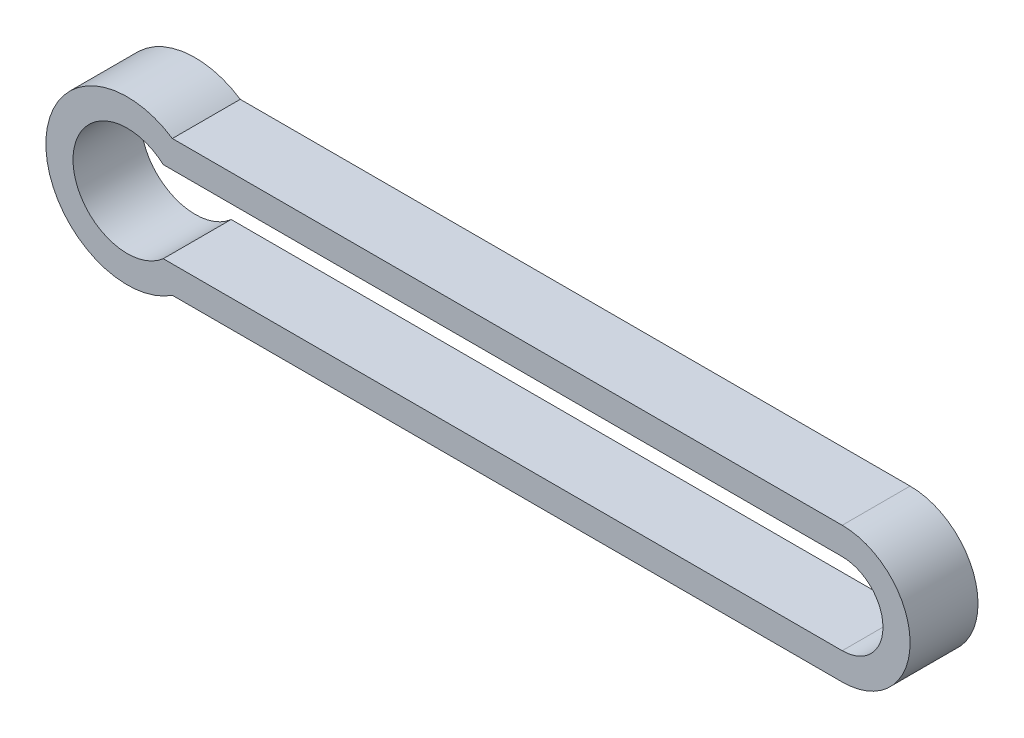
SolidWorks part; units mm, degrees
ref_plane "Front" through (0, 0, 0) normal (0, 0, 1) x (1, 0, 0)
ref_plane "Top" through (0, 0, 0) normal (0, 1, 0) x (1, 0, 0)
ref_plane "Right" through (0, 0, 0) normal (1, 0, 0) x (0, 0, -1)
sketch "草图1" plane through (0, 0, 0) normal (0, 0, 1) x (1, 0, 0)
  line L0 (2.6458, 3) -> (52.6458, 3)
  line L6 (2.6458, -3) -> (52.6458, -3)
  line L9 (52.6458, -5) -> (3.3166, -5)
  line L10 (52.6458, 5) -> (3.3166, 5)
  arc A1 (2.6458, 3) -> (2.6458, -3) centre (0, 0) ccw
  arc A9 (52.6458, -3) -> (52.6458, 3) centre (52.6458, 0) ccw
  arc A11 (3.3166, 5) -> (3.3166, -5) centre (0, 0) ccw
  arc A12 (52.6458, -5) -> (52.6458, 5) centre (52.6458, 0) ccw
  point P4 (48.1176, 0)
  point P6 (0, 4)
  point P7 (49.9977, 3.5306)
  point P9 (0, -3)
  point P10 (50.6439, -2.5738)
  point P11 (0, 3)
  point P12 (50.6439, 2.5738)
extrude "凸台-拉伸1" add sketch "草图1" along normal blind 5
